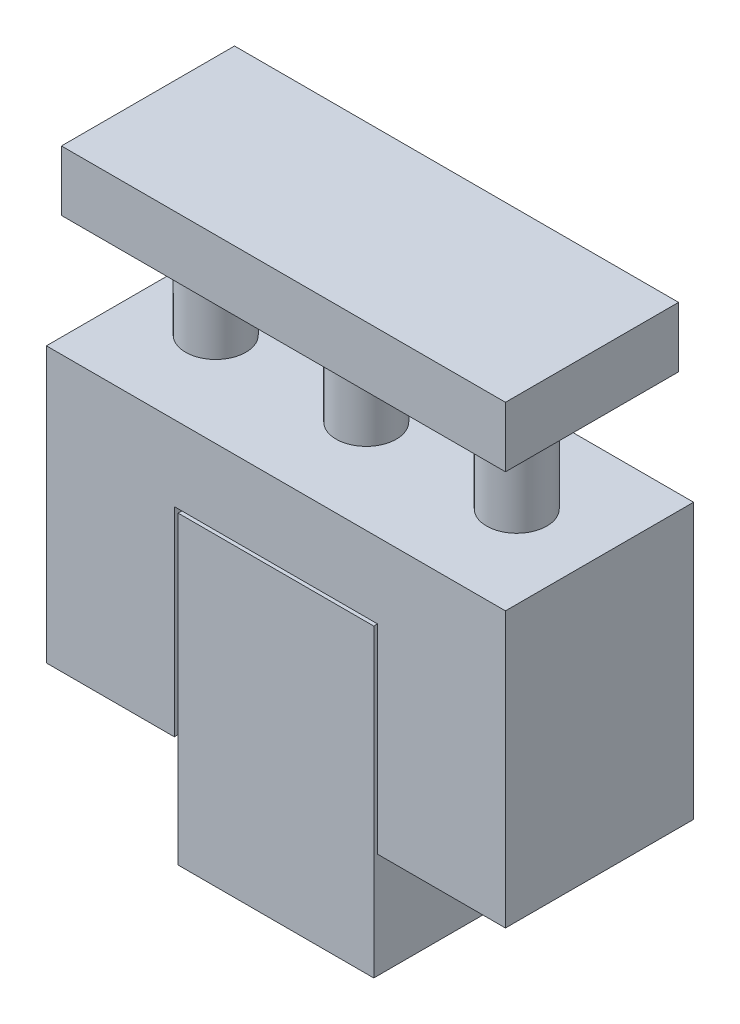
SolidWorks part; units mm, degrees
ref_plane "前视基准面" through (0, 0, 0) normal (0, 0, 1) x (1, 0, 0)
ref_plane "上视基准面" through (0, 0, 0) normal (0, 1, 0) x (1, 0, 0)
ref_plane "右视基准面" through (0, 0, 0) normal (1, 0, 0) x (0, 0, -1)
sketch "草图1" plane through (0, 0, 0) normal (0, 0, 1) x (1, 0, 0)
  line L1 (-26, 40.5) -> (26, 40.5)
  line L2 (-26, 40.5) -> (-26, -40.5)
  line L3 (-26, -40.5) -> (26, -40.5)
  line L4 (26, 40.5) -> (26, -40.5)
  line L5 (-26, 40.5) -> (26, -40.5) construction
  line L6 (-26, -40.5) -> (26, 40.5) construction
  point P0 (0, 0)
  dimension "D1" = 52
  dimension "D2" = 81
extrude "凸台-拉伸1" add sketch "草图1" along normal blind 50
sketch "草图2" plane through (0, 0, 50) normal (0, 0, 1) x (1, 0, 0)
  line L0 (0, 69.6276) -> (0, -61.0908) construction
  line L1 (-61, -11.5) -> (-27, -11.5)
  line L2 (-61, -11.5) -> (-61, 61.5)
  line L3 (-61, 61.5) -> (61, 61.5)
  line L9 (27, 41.5) -> (-27, 41.5)
  line L10 (-27, 41.5) -> (-27, -11.5)
  line L11 (61, -11.5) -> (61, 61.5)
  line L12 (61, -11.5) -> (27, -11.5)
  line L13 (27, 41.5) -> (27, -11.5)
  line L14 (-26, 40.5) -> (-26, -40.5) construction
  line L15 (26, 40.5) -> (-26, 40.5) construction
  point P5 (0, 61.5)
  point P13 (0, 41.5)
  dimension "D1" = 122
  dimension "D2" = 1
  dimension "D3" = 20
  dimension "D4" = 1
  dimension "D5" = 52
extrude "凸台-拉伸2" add sketch "草图2" against normal blind 50 separate body
sketch "草图3" plane through (0, 61.5, 0) normal (0, 1, 0) x (1, 0, 0)
  line L1 (-61, 0) -> (-61, -50) construction
  circle A0 centre (-41, -25) radius 8
  circle A1 centre (-1, -25) radius 8
  circle A2 centre (39, -25) radius 8
  point P6 (-61, -25)
  dimension "D1" = 16
  dimension "D2" = 0
  dimension "D3" = 20
  dimension "D4" = 3
extrude "凸台-拉伸3" add sketch "草图3" along normal blind 30
sketch "草图4" plane through (0, 91.5, 0) normal (0, 1, 0) x (1, 0, 0)
  line L0 (-61, 0) -> (-61, -50) construction
  line L1 (-59, -2) -> (59, -2)
  line L2 (-59, -2) -> (-59, -48)
  line L3 (-59, -48) -> (59, -48)
  line L4 (59, -2) -> (59, -48)
  point P4 (0, -2)
  point P6 (-59, -25)
  point P9 (-61, -25)
  dimension "D1" = 118
  dimension "D2" = 46
  dimension "D3" = 0
  dimension "D4" = 0
extrude "凸台-拉伸4" add sketch "草图4" along normal blind 16
